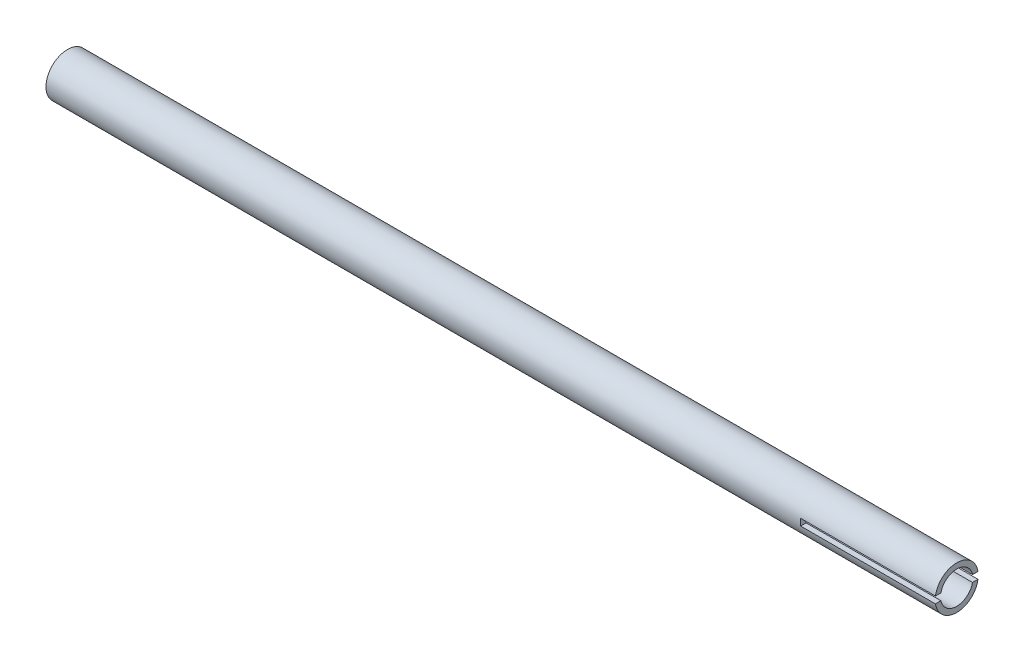
SolidWorks part; units mm, degrees
material "1.0037 (S235JR)"
ref_plane "Front Plane" through (0, 0, 0) normal (0, 0, 1) x (1, 0, 0)
ref_plane "Top Plane" through (0, 0, 0) normal (0, 1, 0) x (1, 0, 0)
ref_plane "Right Plane" through (0, 0, 0) normal (1, 0, 0) x (0, 0, -1)
sketch "Sketch1" plane through (0, 0, 0) normal (1, 0, 0) x (0, 0, -1)
  circle A0 centre (0, 0) radius 8
  circle A1 centre (0, 0) radius 6
  dimension "D1" = 16
  dimension "D2" = 2
extrude "Boss-Extrude1" add sketch "Sketch1" along normal mid plane 330
sketch "Sketch2" plane through (0, 0, 0) normal (0, 0, 1) x (1, 0, 0)
  line L0 (165, -8) -> (165, 8) construction
  line L1 (165, 1.25) -> (115, 1.25)
  line L2 (165, 1.25) -> (165, -1.25)
  line L3 (165, -1.25) -> (115, -1.25)
  line L4 (115, 1.25) -> (115, -1.25)
  line L5 (165, 0) -> (0, 0) construction
  dimension "D1" = 2.5
  dimension "D2" = 50
extrude "Cut-Extrude1" cut sketch "Sketch2" against normal through all both and the other way through all
ref_plane "Plane1" through (0, 0, 8) normal (0, 0, 1) x (1, 0, 0)
